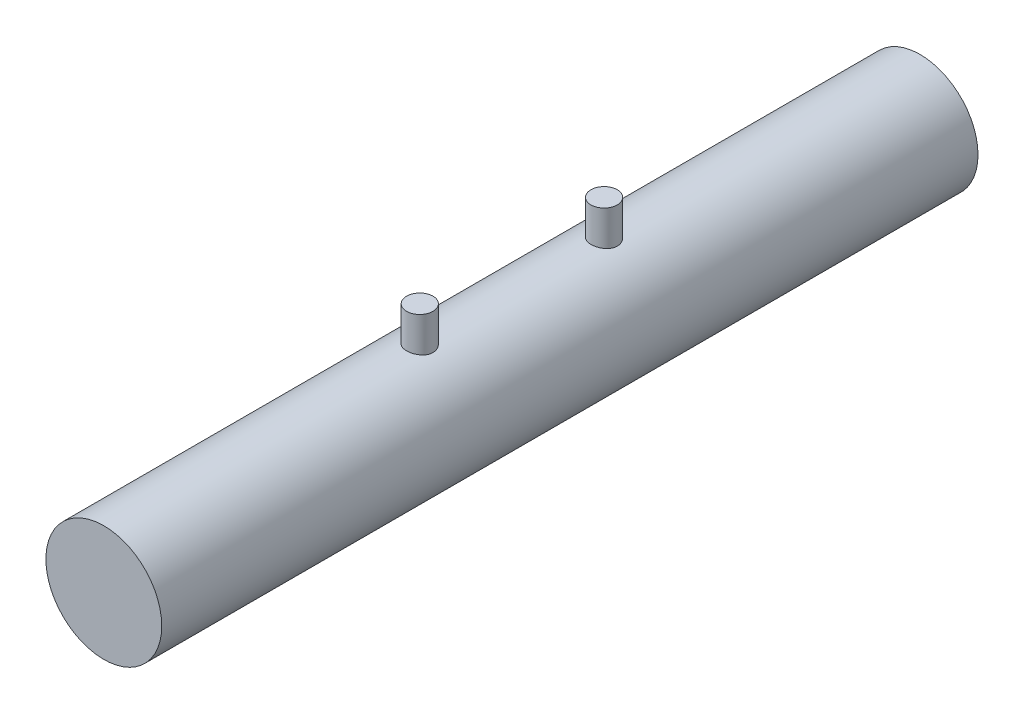
SolidWorks part; units mm, degrees
ref_plane "Plano frontal" through (0, 0, 0) normal (0, 0, 1) x (1, 0, 0)
ref_plane "Plano superior" through (0, 0, 0) normal (0, 1, 0) x (1, 0, 0)
ref_plane "Plano direito" through (0, 0, 0) normal (1, 0, 0) x (0, 0, -1)
sketch "Esboço1" plane through (0, 0, 0) normal (0, 0, 1) x (1, 0, 0)
  circle A0 centre (0, 0) radius 110
  dimension "D1" = 220
extrude "Ressalto-extrusão1" add sketch "Esboço1" along normal blind 1550
ref_plane "Plano1" through (0, 175, 0) normal (0, 1, 0) x (1, 0, 0)
sketch "Esboço3" plane through (0, 175, 0) normal (0, 1, 0) x (1, 0, 0)
  line L0 (0, 0) -> (0, -1550) construction
  line L1 (-110, -1550) -> (110, -1550) construction
  line L2 (110, 0) -> (-110, 0) construction
  circle A0 centre (0, -600) radius 25
  circle A1 centre (0, -950) radius 25
  dimension "D1" = 50
  dimension "D2" = 50
  dimension "D3" = 600
  dimension "D4" = 600
extrude "Ressalto-extrusão2" add sketch "Esboço3" against normal up to surface (65 mm away)
ref_plane "Plano2" through (0, 0, 775) normal (0, 0, 1) x (1, 0, 0)
